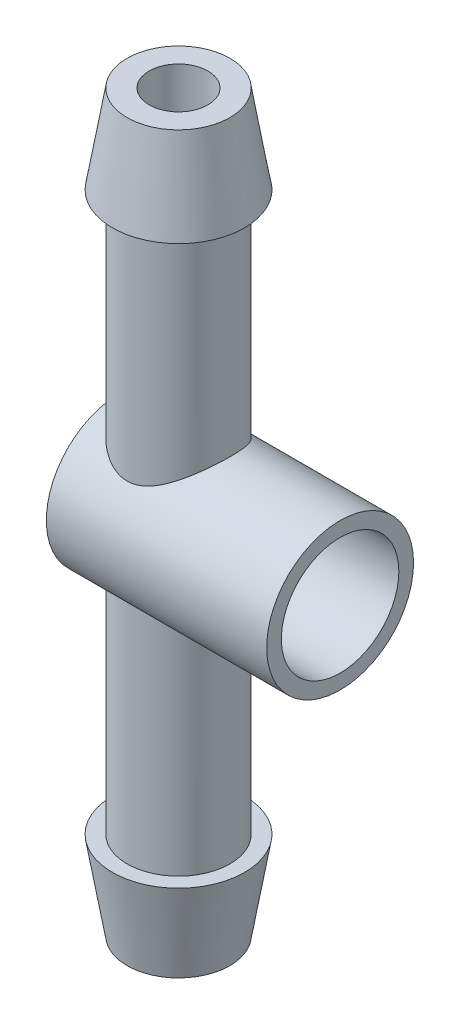
SolidWorks part; units mm, degrees
ref_plane "Front Plane" through (0, 0, 0) normal (0, 0, 1) x (1, 0, 0)
ref_plane "Top Plane" through (0, 0, 0) normal (0, 1, 0) x (1, 0, 0)
ref_plane "Right Plane" through (0, 0, 0) normal (1, 0, 0) x (0, 0, -1)
sketch "Sketch3" plane through (0, 0, 0) normal (0, 0, 1) x (1, 0, 0)
  line L0 (2.5, -25) -> (2.5, 25)
  line L1 (0, 0) -> (2.5, 0)
  line L2 (0, 0) -> (0, 6.2205)
  line L3 (0, 6.2205) -> (2.5, 6.2205)
  line L4 (2.5, 0) -> (2.5, 6.2205)
  line L5 (2.5, 25) -> (3.5, 25)
  line L6 (3.5, 25) -> (4.5, 19)
  line L7 (4.5, 19) -> (3.5, 19)
  line L8 (3.5, 19) -> (3.5, -19)
  line L9 (3.5, 0) -> (2.5, 0)
  line L10 (4.5, -19) -> (3.5, -19)
  line L11 (3.5, -25) -> (4.5, -19)
  line L12 (2.5, -25) -> (3.5, -25)
  line L13 (2.5, 25) -> (2.5, -25)
  line L14 (2.5, 25) -> (0, 25)
  line L15 (2.5, -25) -> (0, -25)
  line L16 (0, 25) -> (0, -25)
  dimension "D1" = 6
  dimension "D2" = 1
  dimension "D3" = 25
  dimension "D4" = 1
  dimension "D5" = 2.5
  dimension "D6" = 6.2205
revolve "Revolve1" add sketch "Sketch3" angle 360 about L2
sketch "Sketch5" plane through (0, 0, 0) normal (1, 0, 0) x (0, 0, -1)
  circle A0 centre (0, 0) radius 5
  dimension "D1" = 10
extrude "Boss-Extrude2" add sketch "Sketch5" along normal mid plane 15 from offset 3.5
sketch "Sketch6" plane through (11, 0, 0) normal (1, 0, 0) x (0, 0, -1)
  circle A0 centre (0, 0) radius 4
  circle A1 centre (0, 0) radius 5 construction
  dimension "D1" = 1
extrude "Cut-Extrude1" cut sketch "Sketch6" against normal blind 13.5
sketch "Sketch7" plane through (0, -25, 0) normal (0, -1, 0) x (1, 0, 0)
  circle A0 centre (0, 0) radius 2
  point P3 (0, 0)
  point P5 (0, 0)
  dimension "D1" = 4
extrude "Cut-Extrude2" cut sketch "Sketch7" along direction (0, -1, 0) on the side against the normal up to surface (50 mm away)
